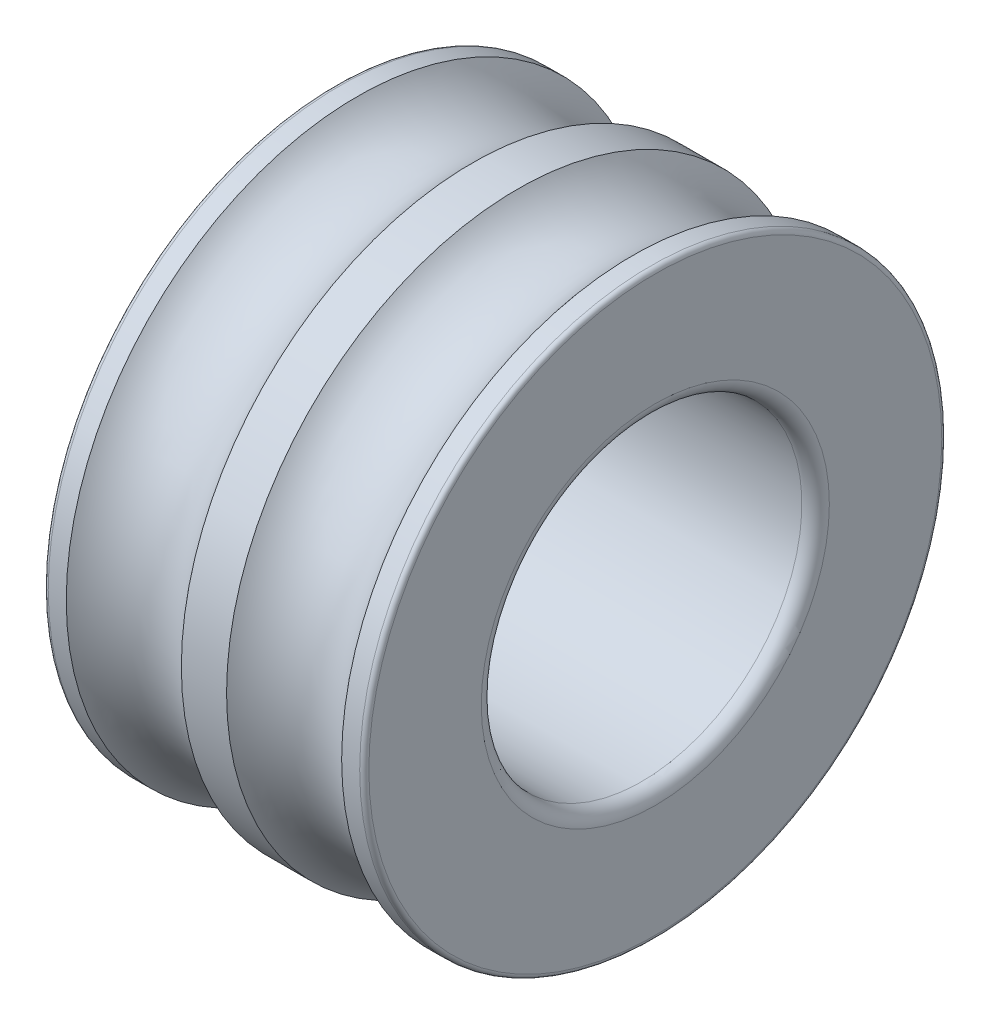
SolidWorks part; units mm, degrees
ref_plane "Front Plane" through (0, 0, 0) normal (0, 0, 1) x (1, 0, 0)
ref_plane "Top Plane" through (0, 0, 0) normal (0, 1, 0) x (1, 0, 0)
ref_plane "Right Plane" through (0, 0, 0) normal (1, 0, 0) x (0, 0, -1)
ref_plane "Plane1" through (0, 0, 0) normal (0, 0, 1) x (1, 0, 0)
sketch "Sketch1" plane through (0, 0, 0) normal (0, 0, 1) x (1, 0, 0)
  line L0 (0, 6.2545) -> (0, 3.8)
  line L1 (0.3, 3.5) -> (6.7, 3.5)
  line L2 (7, 3.8) -> (7, 6.2545)
  line L3 (6.9, 6.3545) -> (6.5063, 6.3545)
  line L4 (3.9937, 6.3545) -> (3.0063, 6.3545)
  line L5 (0.4937, 6.3545) -> (0.1, 6.3545)
  line L6 (50, 0) -> (-50, 0) construction
  arc A0 (0, 3.8) -> (0.3, 3.5) centre (0.3, 3.8) ccw
  arc A1 (6.7, 3.5) -> (7, 3.8) centre (6.7, 3.8) ccw
  arc A2 (7, 6.2545) -> (6.9, 6.3545) centre (6.9, 6.2545) ccw
  arc A3 (6.5063, 6.3545) -> (3.9937, 6.3545) centre (5.25, 7.325) cw
  arc A4 (3.0063, 6.3545) -> (0.4937, 6.3545) centre (1.75, 7.325) cw
  arc A5 (0.1, 6.3545) -> (0, 6.2545) centre (0.1, 6.2545) ccw
revolve "Revolve1" add sketch "Sketch1" angle 360 about L6
